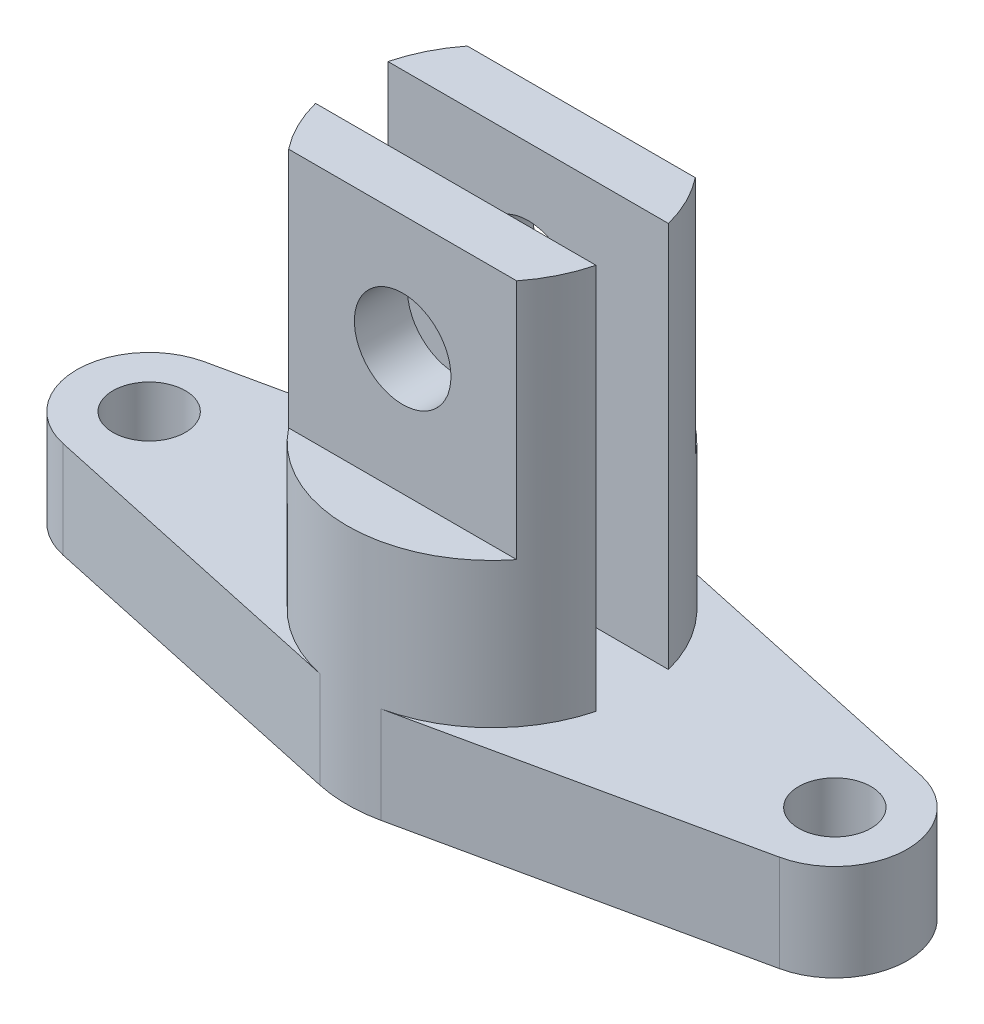
SolidWorks part; units mm, degrees
ref_plane "Alzado" through (0, 0, 0) normal (0, 0, 1) x (1, 0, 0)
ref_plane "Planta" through (0, 0, 0) normal (0, 1, 0) x (1, 0, 0)
ref_plane "Vista lateral" through (0, 0, 0) normal (1, 0, 0) x (0, 0, -1)
sketch "Croquis1" plane through (0, 0, 0) normal (0, 1, 0) x (1, 0, 0)
  line L0 (6.338, 1.3699) -> (74.169, 16.0314)
  line L1 (74.169, 45.3542) -> (6.338, 60.0156)
  line L2 (-6.338, 60.0156) -> (-74.169, 45.3542)
  line L3 (-74.169, 16.0314) -> (-6.338, 1.3699)
  arc A0 (74.169, 16.0314) -> (74.169, 45.3542) centre (71, 30.6928) ccw
  arc A1 (-74.169, 45.3542) -> (-74.169, 16.0314) centre (-71, 30.6928) ccw
  arc A2 (6.338, 1.3699) -> (-6.338, 1.3699) centre (0, 30.6928) cw
  arc A3 (6.338, 60.0156) -> (-6.338, 60.0156) centre (0, 30.6928) ccw
  circle A4 centre (-71, 30.6928) radius 7.5
  circle A5 centre (71, 30.6928) radius 7.5
  point P0 (0, 0)
  point P13 (0, 0)
  dimension "D2" = 15
  dimension "D3" = 30
  dimension "D4" = 15
  dimension "D1" = 142
extrude "Saliente-Extruir1" add sketch "Croquis1" along normal blind 20
sketch "Croquis2" plane through (0, 20, 0) normal (0, 1, 0) x (1, 0, 0)
  line L0 (-29.0474, 23.1928) -> (29.0474, 23.1928)
  line L1 (-29.0474, 38.1928) -> (29.0474, 38.1928)
  arc A0 (-29.0474, 23.1928) -> (29.0474, 23.1928) centre (0, 30.6928) ccw
  arc A1 (-6.338, 1.3699) -> (6.338, 1.3699) centre (0, 30.6928) ccw construction
  arc A2 (29.0474, 38.1928) -> (-29.0474, 38.1928) centre (0, 30.6928) ccw
  dimension "D1" = 15
extrude "Saliente-Extruir2" add sketch "Croquis2" along normal blind 80
sketch "Croquis3" plane through (0, 100, 0) normal (0, 1, 0) x (1, 0, 0)
  line L0 (-23.6167, 49.1928) -> (23.6167, 49.1928)
  line L1 (-23.6167, 12.1928) -> (23.6167, 12.1928)
  arc A0 (-29.0474, 23.1928) -> (29.0474, 23.1928) centre (0, 30.6928) ccw construction
  arc A1 (29.0474, 38.1928) -> (-29.0474, 38.1928) centre (0, 30.6928) ccw construction
  arc A2 (-23.6167, 12.1928) -> (23.6167, 12.1928) centre (0, 30.6928) ccw
  arc A3 (23.6167, 49.1928) -> (-23.6167, 49.1928) centre (0, 30.6928) ccw
  dimension "D1" = 37
extrude "Cortar-Extruir1" cut sketch "Croquis3" against normal blind 50
sketch "Croquis4" plane through (0, 0, -12.1928) normal (0, 0, 1) x (1, 0, 0)
  line L0 (23.6167, 100) -> (-23.6167, 100) construction
  circle A0 centre (0, 76) radius 10
  point P2 (0, 0)
  point P4 (0, 77.4481)
  dimension "D1" = 20
  dimension "D2" = 24
extrude "Cortar-Extruir2" cut sketch "Croquis4" against normal up to surface (37 mm away) up to face at (0, 75, -49.1928)
